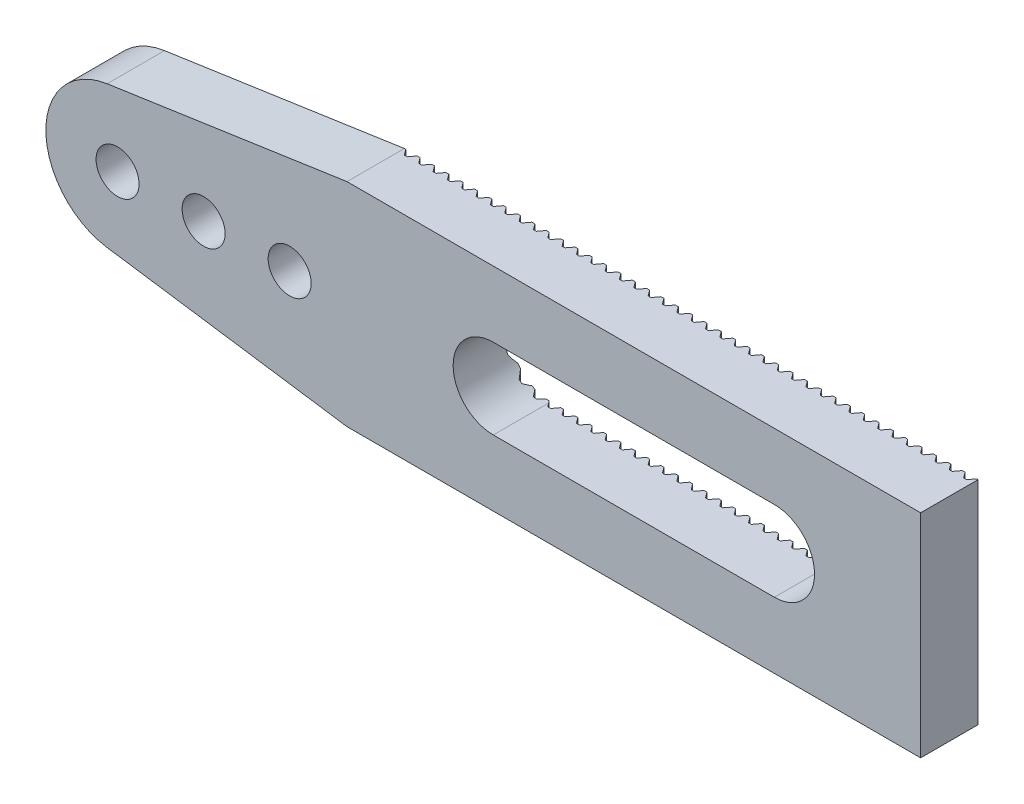
SolidWorks part; units mm, degrees
ref_plane "Face" through (0, 0, 0) normal (0, 0, 1) x (1, 0, 0)
ref_plane "Dessus" through (0, 0, 0) normal (0, 1, 0) x (1, 0, 0)
ref_plane "Droite" through (0, 0, 0) normal (1, 0, 0) x (0, 0, -1)
sketch "Esquisse1" plane through (0, 0, 0) normal (0, 0, 1) x (1, 0, 0)
  line L0 (-10, 3.7) -> (-18.3628, 2.4735)
  line L1 (-10, -3.7) -> (10, -3.7)
  line L2 (-4.9, 0) -> (4.9, 0) construction
  line L3 (-10, 3.7) -> (10, 3.7)
  line L4 (10, -3.7) -> (10, 3.7)
  line L5 (-10, -3.7) -> (10, 3.7) construction
  line L6 (-10, 3.7) -> (10, -3.7) construction
  line L7 (-10, -3.7) -> (-18.3628, -2.4735)
  line L8 (-4.9, 1.4) -> (4.9, 1.4)
  line L9 (-4.9, -1.4) -> (4.9, -1.4)
  arc A0 (-18.3628, 2.4735) -> (-18.3628, -2.4735) centre (-18, 0) ccw
  arc A1 (-4.9, 1.4) -> (-4.9, -1.4) centre (-4.9, 0) ccw
  arc A2 (4.9, -1.4) -> (4.9, 1.4) centre (4.9, 0) ccw
  circle A3 centre (-18, 0) radius 0.75
  circle A4 centre (-15, 0) radius 0.75
  circle A5 centre (-12, 0) radius 0.75
  point P0 (0, 0)
  point P9 (0, 0)
  dimension "D3" = 5
  dimension "D5" = 1.4
  dimension "D7" = 1.5
  dimension "D8" = 3
  dimension "D9" = 3
  dimension "D1" = 7.4
  dimension "D2" = 20
  dimension "D4" = 28
  dimension "D6" = 9.8
extrude "Boss.-Extru.1" add sketch "Esquisse1" along normal blind 2
sketch "Esquisse2" plane through (0, 3.7, 0) normal (0, 1, 0) x (1, 0, 0)
  line L0 (9.95, 0) -> (9.55, 0)
  line L1 (10, 0) -> (-10, 0) construction
  line L2 (9.55, 0) -> (9.7, -0.2)
  line L3 (9.7, -0.2) -> (9.8, -0.2)
  line L4 (9.8, -0.2) -> (9.95, 0)
  line L5 (9.75, 0) -> (9.75, -0.2) construction
  line L6 (10, -2) -> (10, 0) construction
  dimension "D1" = 0.2
  dimension "D2" = 0.4
  dimension "D3" = 0.1
  dimension "D4" = 0.05
extrude "Enlèv. mat.-Extru.1" cut sketch "Esquisse2" against normal through all
pattern_linear "Répétition linéaire1" count 40 spacing 0.5 along (-1, 0, 0) of "Enlèv. mat.-Extru.1"
